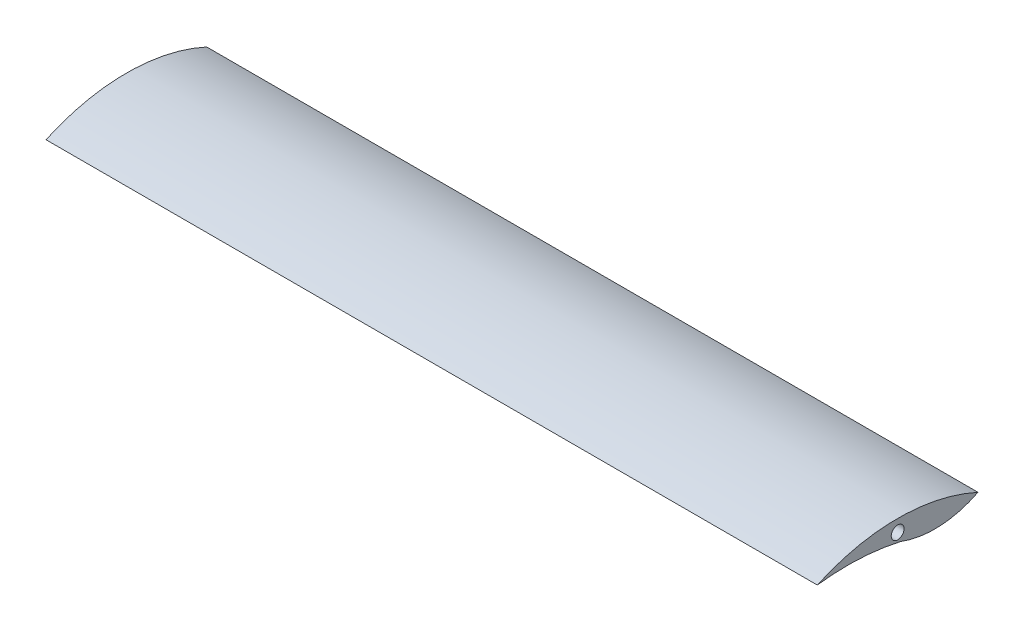
SolidWorks part; units mm, degrees
ref_plane "Front Plane" through (0, 0, 0) normal (0, 0, 1) x (1, 0, 0)
ref_plane "Top Plane" through (0, 0, 0) normal (0, 1, 0) x (1, 0, 0)
ref_plane "Right Plane" through (0, 0, 0) normal (1, 0, 0) x (0, 0, -1)
sketch "Sketch2" plane through (0, 0, 0) normal (1, 0, 0) x (0, 0, -1)
  arc A0 (-77.0066, 0) -> (172.9934, 0) centre (47.9934, -272.7178) cw
  arc A1 (-77.0066, 0) -> (52.516, -6.1858) centre (-29.7314, -369.2307) cw
  arc A2 (52.516, -6.1858) -> (172.9934, 0) centre (105.7599, 133.1407) ccw
  dimension "D1" = 300
  dimension "D2" = 250
extrude "Boss-Extrude2" add sketch "Sketch2" along normal blind 1200
sketch "Sketch4" plane through (0, 0, 0) normal (-1, 0, 0) x (0, 0, 1)
  line L0 (-47.9934, -972.7178) -> (-47.9934, 49027.2822) construction
  line L1 (-1047.9934, 8.4384) -> (48952.0066, 8.4384) construction
  arc A0 (77.0066, 0) -> (-172.9934, 0) centre (-47.9934, -272.7178) ccw construction
  circle A5 centre (-47.9934, 8.4384) radius 10
  point P12 (-47.9934, 27.2822)
  dimension "D1" = 20
extrude "Cut-Extrude2" cut sketch "Sketch4" against normal blind 30
ref_plane "Plane1" through (600, 0, 0) normal (1, 0, 0) x (0, 0, -1)
mirror "Mirror1" about plane through (600, 0, 0) normal (1, 0, 0) of "Cut-Extrude2"
ref_plane "Plane2" through (800, 0, 0) normal (1, 0, 0) x (0, 0, -1)
sketch "Sketch5" plane through (800, 0, 0) normal (1, 0, 0) x (0, 0, -1)
  line L12 (81.4107, -14.0119) -> (85.14, -17.7809)
  line L13 (-983.8478, -24.2478) -> (49016.1522, -24.2478) construction
  line L14 (-983.8478, -52.5558) -> (49016.1522, -52.5558) construction
  line L15 (111.6333, -17.7665) -> (119.8947, -15.3416)
  line L18 (80.9057, -13.6029) -> (81.4107, -14.0119)
  line L19 (119.8947, -15.3416) -> (121.6192, -14.8813)
  line L26 (0, 1.825) -> (0, -28.4827)
  line L27 (34.3691, -2.5464) -> (34.3691, -24.2478)
  arc A13 (80.9057, -13.6029) -> (121.6192, -14.8813) centre (111.1335, 300.1185) ccw
  circle A17 centre (18.0911, -35.8523) radius 10
  arc A19 (52.516, -6.1858) -> (172.9934, 0) centre (105.7599, 133.1407) ccw construction
  arc A20 (85.14, -17.7809) -> (85.935, -18.9583) centre (82.412, -20.4802) cw
  arc A21 (85.935, -18.9583) -> (110.3891, -21.7394) centre (96.6023, -34.0636) ccw
  arc A22 (110.3891, -21.7394) -> (111.6333, -17.7665) centre (112.1961, -20.1241) cw
  circle A23 centre (96.6023, -34.0636) radius 10
  arc A25 (0, -28.4827) -> (34.3691, -24.2478) centre (18.2958, -35.3836) ccw
  arc A31 (0, 1.825) -> (34.3691, -2.5464) centre (-29.7314, -369.2307) cw
  arc A32 (52.516, -6.1858) -> (-77.0066, 0) centre (-29.7314, -369.2307) ccw construction
  dimension "D5" = 20
  dimension "D6" = 20
extrude "Boss-Extrude3" add sketch "Sketch5" against normal blind 20
ref_plane "Plane3" through (613, 0, 0) normal (-1, 0, 0) x (0, 0, 1)
scale "Scale1" scale about centroid uniform scaling yes scale factor 0.15
ref_plane "Plane4" through (572.0648, 0, 0) normal (1, 0, 0) x (0, 0, -1)
sketch "Sketch8" plane through (572.0648, 0, 0) normal (1, 0, 0) x (0, 0, -1)
  line L0 (54.8303, 5.9261) -> (54.8303, 1.3799)
  line L1 (59.9857, 2.0151) -> (59.9857, 5.2704)
  line L2 (67.0419, 3.5505) -> (67.6692, 2.9024)
  line L3 (67.6692, 2.9024) -> (67.7206, 2.8086)
  line L4 (71.5753, 2.9873) -> (72.8145, 3.3511)
  line L5 (59.9857, 5.2704) -> (56.4885, 5.9261)
  line L6 (56.4885, 5.9261) -> (54.8303, 5.9261)
  arc A0 (54.8303, 1.3799) -> (59.9857, 2.0151) centre (57.5747, 0.3448) ccw
  arc A1 (67.7206, 2.8086) -> (67.6013, 2.9852) centre (67.1921, 2.5803) ccw construction
  arc A2 (67.7206, 2.8086) -> (71.3887, 2.3914) centre (69.3206, 0.5428) ccw
  arc A3 (71.3887, 2.3914) -> (71.5753, 2.9873) centre (71.6597, 2.6337) cw
  arc A4 (72.8145, 3.3511) -> (67.0419, 3.5505) centre (70.6943, 25.6234) cw
  circle A5 centre (69.3206, 0.5428) radius 1.5
  circle A6 centre (57.5747, 0.3448) radius 1.4233
extrude "Boss-Extrude4" add sketch "Sketch8" along normal blind 2.5
